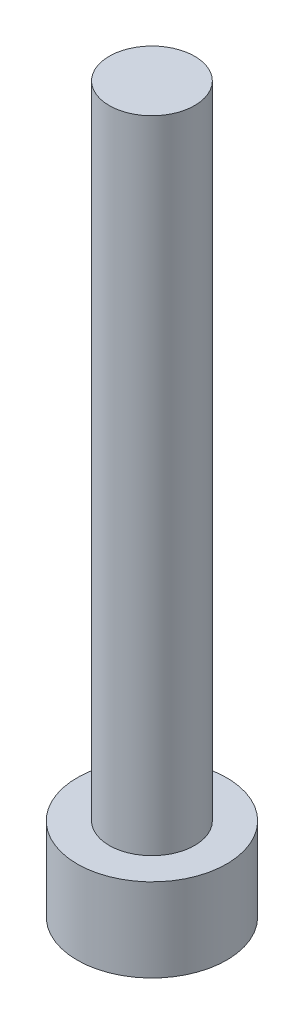
SolidWorks part; units mm, degrees
ref_plane "前视基准面" through (0, 0, 0) normal (0, 0, 1) x (1, 0, 0)
ref_plane "上视基准面" through (0, 0, 0) normal (0, 1, 0) x (1, 0, 0)
ref_plane "右视基准面" through (0, 0, 0) normal (1, 0, 0) x (0, 0, -1)
sketch "草图1" plane through (0, 0, 0) normal (0, 1, 0) x (1, 0, 0)
  circle A0 centre (0, 0) radius 3.5
extrude "凸台-拉伸1" add sketch "草图1" along normal blind 3.9
sketch "草图2" plane through (0, 3.9, 0) normal (0, 1, 0) x (1, 0, 0)
  circle A0 centre (0, 0) radius 2
extrude "凸台-拉伸2" add sketch "草图2" along normal blind 30
sketch "草图3" plane through (0, 0, 0) normal (0, -1, 0) x (1, 0, 0)
  line L1 (1.725, 0) -> (0.8625, 1.4939)
  line L2 (0.8625, 1.4939) -> (-0.8625, 1.4939)
  line L3 (-0.8625, 1.4939) -> (-1.725, 0)
  line L4 (-1.725, 0) -> (-0.8625, -1.4939)
  line L5 (-0.8625, -1.4939) -> (0.8625, -1.4939)
  line L6 (0.8625, -1.4939) -> (1.725, 0)
  circle A0 centre (0, 0) radius 1.4939 construction
extrude "切除-拉伸1" cut sketch "草图3" against normal blind 2.4
